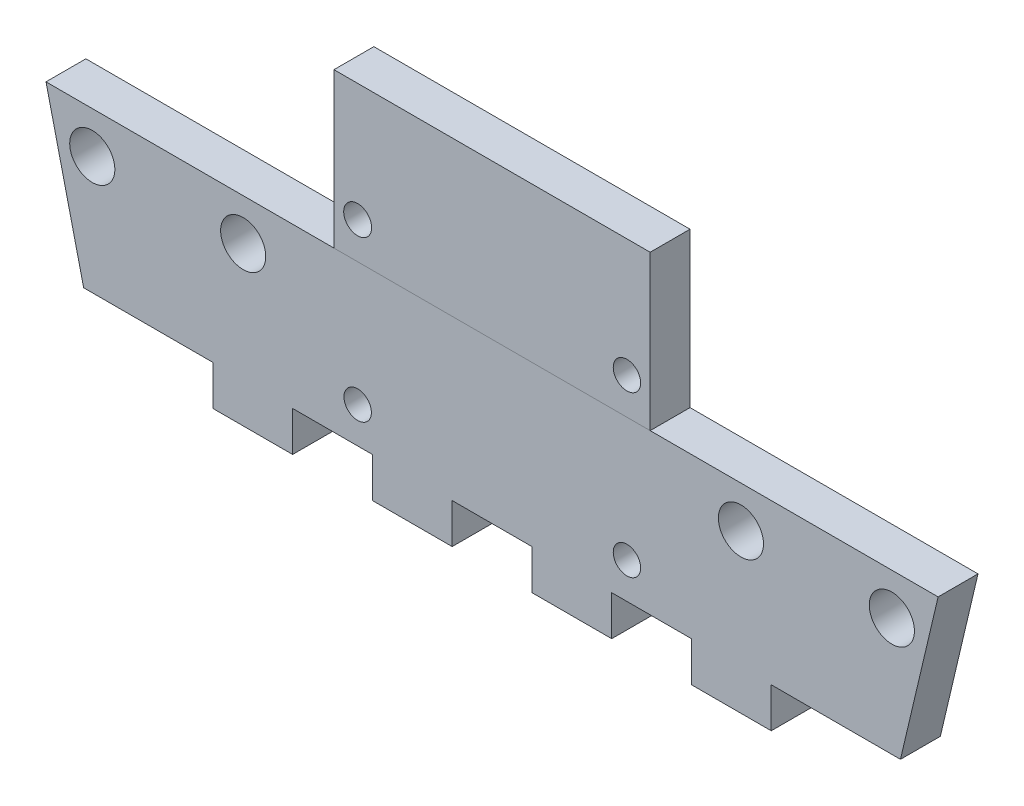
SolidWorks part; units mm, degrees
ref_plane "Front" through (0, 0, 0) normal (0, 0, 1) x (1, 0, 0)
ref_plane "Top" through (0, 0, 0) normal (0, 1, 0) x (1, 0, 0)
ref_plane "Right" through (0, 0, 0) normal (1, 0, 0) x (0, 0, -1)
sketch "Sketch1" plane through (0, 0, 0) normal (0, 0, 1) x (1, 0, 0)
  line L0 (0, 0) -> (65.024, 0)
  line L1 (10.287, -12.7) -> (10.287, -15.875)
  line L2 (68.512, -12.7) -> (-3.488, -12.7)
  line L3 (35.687, -12.7) -> (42.037, -12.7)
  line L4 (32.512, 0) -> (32.512, -12.7) construction
  line L5 (35.687, -12.7) -> (35.687, -15.875)
  line L6 (35.687, -15.875) -> (42.037, -15.875)
  line L7 (42.037, -12.7) -> (42.037, -15.875)
  line L8 (48.387, -12.7) -> (54.737, -12.7)
  line L9 (48.387, -12.7) -> (48.387, -15.875)
  line L10 (48.387, -15.875) -> (54.737, -15.875)
  line L11 (54.737, -12.7) -> (54.737, -15.875)
  line L12 (16.637, -15.875) -> (10.287, -15.875)
  line L13 (16.637, -12.7) -> (16.637, -15.875)
  line L14 (16.637, -12.7) -> (10.287, -12.7)
  line L15 (22.987, -12.7) -> (22.987, -15.875)
  line L16 (29.337, -15.875) -> (22.987, -15.875)
  line L17 (29.337, -12.7) -> (29.337, -15.875)
  line L18 (29.337, -12.7) -> (22.987, -12.7)
  line L19 (4.9582, 0) -> (4.9582, -12.7) construction
  line L20 (4.9582, -6.35) -> (62.52, -6.35) construction
  line L21 (29.337, 0) -> (22.987, 0)
  line L22 (29.337, 0) -> (29.337, 3.175)
  line L23 (29.337, 3.175) -> (22.987, 3.175)
  line L24 (22.987, 0) -> (22.987, 3.175)
  line L25 (16.637, 0) -> (10.287, 0)
  line L26 (16.637, 0) -> (16.637, 3.175)
  line L27 (16.637, 3.175) -> (10.287, 3.175)
  line L28 (54.737, 0) -> (54.737, 3.175)
  line L29 (48.387, 3.175) -> (54.737, 3.175)
  line L30 (48.387, 0) -> (48.387, 3.175)
  line L31 (48.387, 0) -> (54.737, 0)
  line L32 (42.037, 0) -> (42.037, 3.175)
  line L33 (35.687, 3.175) -> (42.037, 3.175)
  line L34 (35.687, 0) -> (35.687, 3.175)
  line L35 (35.687, 0) -> (42.037, 0)
  line L36 (10.287, 0) -> (10.287, 3.175)
  line L37 (0, 0) -> (0, -12.7)
  line L38 (65.024, 0) -> (65.024, -12.7)
  line L39 (0, -12.7) -> (-2.9972, 0)
  line L40 (-2.9972, 0) -> (0, 0)
  line L41 (68.0212, 0) -> (65.024, 0)
  line L42 (65.024, -12.7) -> (68.0212, 0)
  dimension "D1" = 65.024
  dimension "D2" = 72
  dimension "D3" = 6.35
  dimension "D4" = 12.7
  dimension "D5" = 6.35
  dimension "D6" = 6.35
  dimension "D7" = 3.175
  dimension "D8" = 3.175
  dimension "D9" = 3.175
  dimension "D10" = 2.9972
extrude "Boss-Extrude1" add sketch "Sketch1" along normal blind 3.175
sketch "Sketch2" plane through (0, 0, 3.175) normal (0, 0, 1) x (1, 0, 0)
  line L1 (0, 5.9132) -> (65.6031, 5.9132)
  line L2 (0, 5.9132) -> (0, 0)
  line L3 (0, 0) -> (65.6031, 0)
  line L4 (65.6031, 5.9132) -> (65.6031, 0)
extrude "Cut-Extrude2" cut sketch "Sketch2" against normal blind 10
sketch "Sketch3" plane through (0, 0, 3.175) normal (0, 0, 1) x (1, 0, 0)
  line L0 (-2.9972, 0) -> (68.0212, 0) construction
  line L1 (19.9263, 12.3) -> (45.0977, 12.3)
  line L2 (19.9263, 12.3) -> (19.9263, 0)
  line L3 (19.9263, 0) -> (45.0977, 0)
  line L4 (45.0977, 12.3) -> (45.0977, 0)
  line L5 (32.512, 12.3) -> (32.512, 0) construction
  line L6 (32.512, -12.7) -> (32.512, 0) construction
  line L7 (35.687, -12.7) -> (29.337, -12.7) construction
  line L9 (22.987, -12.7) -> (16.637, -12.7) construction
  dimension "D1" = 25.1714
  dimension "D2" = 25
  dimension "D3" = 0
  dimension "D4" = 0
extrude "Boss-Extrude2" add sketch "Sketch3" against normal blind 3.175 separate body
sketch "Sketch4" plane through (0, 0, 3.175) normal (0, 0, 1) x (1, 0, 0)
  line L0 (20.0325, 20.3) -> (44.7919, 20.3) construction
  line L1 (22.987, -12.7) -> (16.637, -12.7) construction
  dimension "D1" = 33
sketch "Sketch6" plane through (0, 0, 0) normal (0, 0, -1) x (-1, 0, 0)
  circle A0 centre (-43.2506, 2.902) radius 1.0922
  circle A1 centre (-21.813, 2.902) radius 1.1121
  circle A2 centre (-21.813, -9.8488) radius 1.0922
  circle A3 centre (-43.2506, -9.8488) radius 1.0922
extrude "Cut-Extrude3" cut sketch "Sketch6" against normal blind 3.175
sketch "Sketch8" plane through (0, 0, 0) normal (0, 0, -1) x (-1, 0, 0)
  circle A0 centre (-64.3382, -3.302) radius 1.797
  circle A1 centre (-52.324, -3.302) radius 1.7971
  circle A2 centre (-12.7, -3.302) radius 1.797
  circle A3 centre (-0.6858, -3.302) radius 1.797
extrude "Cut-Extrude4" cut sketch "Sketch8" against normal blind 3.175
